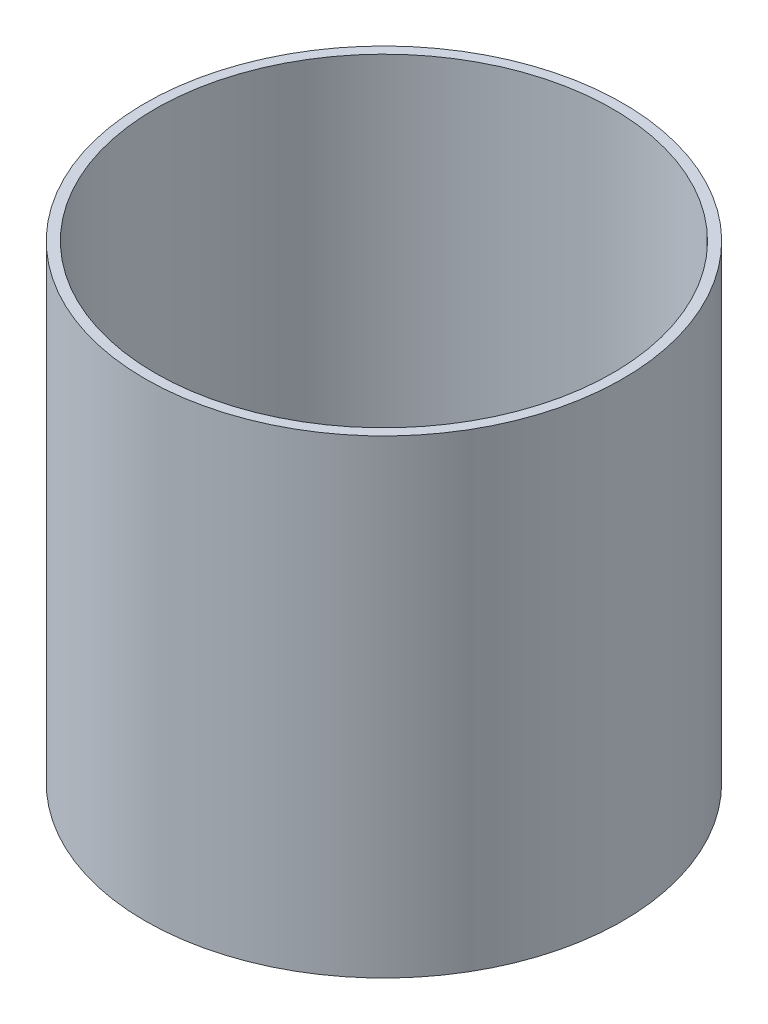
SolidWorks part; units mm, degrees
ref_plane "Front Plane" through (0, 0, 0) normal (0, 0, 1) x (1, 0, 0)
ref_plane "Top Plane" through (0, 0, 0) normal (0, 1, 0) x (1, 0, 0)
ref_plane "Right Plane" through (0, 0, 0) normal (1, 0, 0) x (0, 0, -1)
sketch "Sketch1" plane through (0, 0, 0) normal (0, 1, 0) x (1, 0, 0)
  circle A0 centre (0, 0) radius 21.08
  circle A1 centre (0, 0) radius 22
  dimension "D1" = 44
  dimension "D2" = 42.16
extrude "Boss-Extrude1" add sketch "Sketch1" along normal blind 43.25
